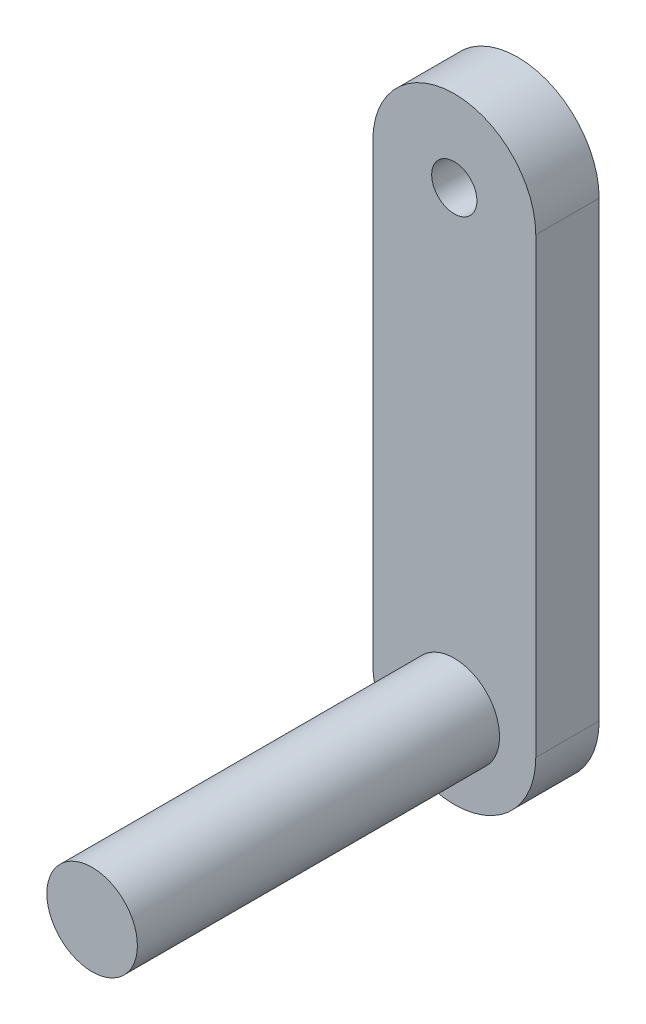
SolidWorks part; units mm, degrees
ref_plane "Front Plane" through (0, 0, 0) normal (0, 0, 1) x (1, 0, 0)
ref_plane "Top Plane" through (0, 0, 0) normal (0, 1, 0) x (1, 0, 0)
ref_plane "Right Plane" through (0, 0, 0) normal (1, 0, 0) x (0, 0, -1)
sketch "Sketch1" plane through (0, 0, 0) normal (0, 0, 1) x (1, 0, 0)
  line L0 (-9, 50) -> (-9, 0)
  line L1 (9, 50) -> (9, 0)
  arc A0 (-9, 50) -> (9, 50) centre (0, 50) cw
  arc A1 (-9, 0) -> (9, 0) centre (0, 0) ccw
  dimension "D2" = 9
  dimension "D1" = 50
extrude "Boss-Extrude1" add sketch "Sketch1" along normal blind 7
sketch "Sketch2" plane through (0, 0, 7) normal (0, 0, 1) x (1, 0, 0)
  circle A0 centre (0, 0) radius 5
  dimension "D1" = 10
extrude "Boss-Extrude2" add sketch "Sketch2" along normal blind 40
hole_wizard "M6 Tapped Hole1" positions "Sketch4" profile "Sketch3" tap size "M6" standard "ISO"
sketch "Sketch4" plane through (0, 0, 0) normal (0, 0, -1) x (-1, 0, 0)
  point P0 (0, 50)
  dimension "D1" = 50
sketch "Sketch3" plane through (0, 50, 0) normal (1, 0, 0) x (0, 1, 0)
  line L0 (0, 0) -> (0, 16.5022)
  line L1 (0, 16.5022) -> (2.5, 15)
  line L2 (2.5, 15) -> (2.5, 0)
  line L5 (2.5, 0) -> (0, 0)
  line L10 (0, 16.5022) -> (-2.5, 15) construction
  line L11 (0, -6.35) -> (0, 107.95) construction
  dimension "Tap Drill Dia." = 5
  dimension "Tap Drill Depth" = 15
  dimension "Drill Angle" = 118
cosmetic thread "Hole Thread1" parameters "D1"=7, "D2"=6
